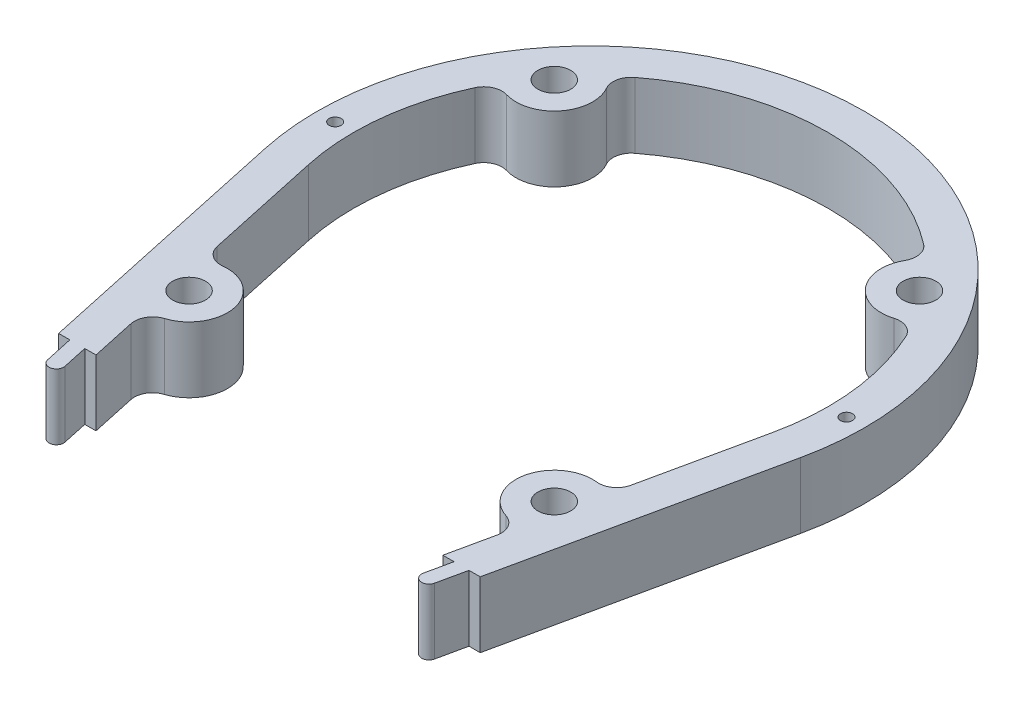
SolidWorks part; units mm, degrees
ref_plane "Front Plane" through (0, 0, 0) normal (0, 0, 1) x (1, 0, 0)
ref_plane "Top Plane" through (0, 0, 0) normal (0, 1, 0) x (1, 0, 0)
ref_plane "Right Plane" through (0, 0, 0) normal (1, 0, 0) x (0, 0, -1)
sketch "Sketch1" plane through (0, 0, 0) normal (0, 1, 0) x (1, 0, 0)
  line L0 (-57.7171, -88) -> (-54.6479, -88)
  line L1 (-54.6479, -88) -> (-52.9727, -95.7532)
  line L2 (-49.0629, -94.9085) -> (-50.5556, -88)
  line L3 (-50.5556, -88) -> (-47.4864, -88)
  line L4 (-47.4864, -88) -> (-50.1213, -75.805)
  line L5 (-56.6356, -45.6549) -> (-63.5339, -13.7273)
  line L6 (63.5339, -13.7273) -> (56.6356, -45.6549)
  line L7 (50.1213, -75.805) -> (47.4864, -88)
  line L8 (47.4864, -88) -> (50.5556, -88)
  line L9 (50.5556, -88) -> (49.0629, -94.9085)
  line L10 (52.9727, -95.7532) -> (54.6479, -88)
  line L11 (54.6479, -88) -> (57.7171, -88)
  line L12 (57.7171, -88) -> (73.3084, -15.8392)
  line L13 (-73.3084, -15.8392) -> (-57.7171, -88)
  circle A0 centre (-50, -60) radius 4.5
  circle A1 centre (50, -60) radius 4.5
  circle A2 centre (70, 0) radius 1.65
  circle A3 centre (50, 40) radius 4.5
  circle A4 centre (-50, 40) radius 4.5
  circle A5 centre (-70, 0) radius 1.65
  arc A6 (-52.9727, -95.7532) -> (-49.0629, -94.9085) centre (-51.0178, -95.3308) ccw
  arc A7 (-46.7714, -69.9913) -> (-50.1213, -75.805) centre (-45.234, -74.7491) ccw
  arc A8 (-46.7714, -69.9913) -> (-51.1844, -49.567) centre (-50, -60) ccw
  arc A9 (-56.6356, -45.6549) -> (-51.1844, -49.567) centre (-51.7484, -44.5989) ccw
  arc A10 (-59.0098, 27.2553) -> (-63.5339, -13.7273) centre (0, 0) ccw
  arc A11 (-53.0284, 29.9462) -> (-59.0098, 27.2553) centre (-54.4705, 25.1587) ccw
  arc A12 (-53.0284, 29.9462) -> (-40.8562, 45.1615) centre (-50, 40) ccw
  arc A13 (-39.5439, 51.5876) -> (-40.8562, 45.1615) centre (-36.502, 47.6194) ccw
  arc A14 (39.5439, 51.5876) -> (-39.5439, 51.5876) centre (0, 0) ccw
  arc A15 (40.8562, 45.1615) -> (39.5439, 51.5876) centre (36.502, 47.6194) ccw
  arc A16 (40.8562, 45.1615) -> (53.0284, 29.9462) centre (50, 40) ccw
  arc A17 (59.0098, 27.2553) -> (53.0284, 29.9462) centre (54.4705, 25.1587) ccw
  arc A18 (63.5339, -13.7273) -> (59.0098, 27.2553) centre (0, 0) ccw
  arc A19 (51.1844, -49.567) -> (56.6356, -45.6549) centre (51.7484, -44.5989) ccw
  arc A20 (51.1844, -49.567) -> (46.7714, -69.9913) centre (50, -60) ccw
  arc A21 (50.1213, -75.805) -> (46.7714, -69.9913) centre (45.234, -74.7491) ccw
  arc A22 (49.0629, -94.9085) -> (52.9727, -95.7532) centre (51.0178, -95.3308) ccw
  arc A23 (73.3084, -15.8392) -> (-73.3084, -15.8392) centre (0, 0) ccw
  dimension "D1" = 6
  dimension "D2" = 6
  dimension "D3" = 6
  dimension "D4" = 6
  dimension "D5" = 70
  dimension "D6" = 70
  dimension "D7" = 75
  dimension "D8" = 65
extrude "Boss-Extrude1" add sketch "Sketch1" along normal blind 18
